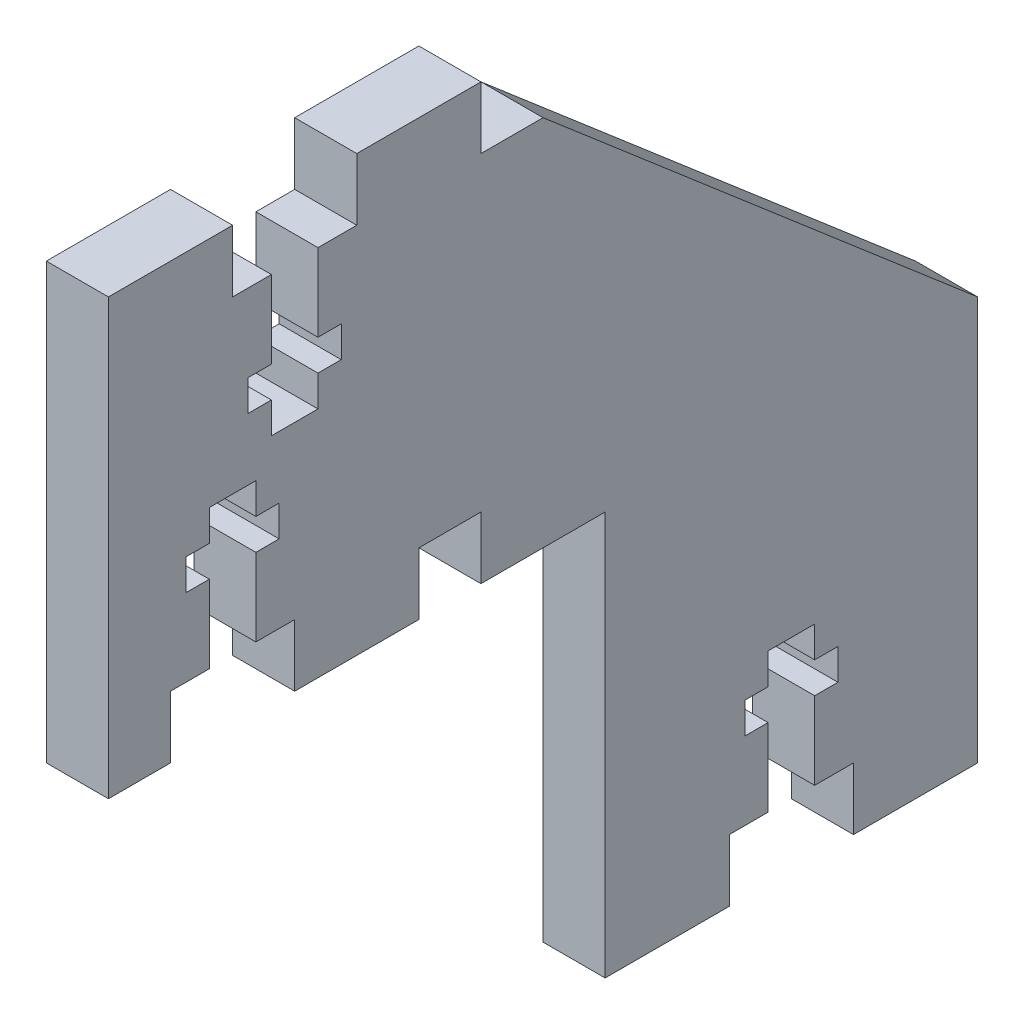
SolidWorks part; units mm, degrees
ref_plane "Front Plane" through (0, 0, 0) normal (0, 0, 1) x (1, 0, 0)
ref_plane "Top Plane" through (0, 0, 0) normal (0, 1, 0) x (1, 0, 0)
ref_plane "Right Plane" through (0, 0, 0) normal (1, 0, 0) x (0, 0, -1)
sketch "Sketch1" plane through (0, 0, 0) normal (1, 0, 0) x (0, 0, -1)
  line L0 (12.7, 44.45) -> (12.7, 38.1)
  line L1 (0, 0) -> (44.45, 0)
  line L2 (0, 0) -> (0, 44.45)
  line L3 (0, 44.45) -> (44.45, 44.45)
  line L4 (44.45, 0) -> (44.45, 44.45)
  line L5 (12.7, 38.1) -> (25.4, 38.1)
  line L6 (6.35, 0) -> (6.35, 6.35)
  line L7 (6.35, 6.35) -> (19.05, 6.35)
  line L8 (19.05, 6.35) -> (19.05, 0)
  line L9 (31.75, 0) -> (31.75, 6.35)
  line L10 (31.75, 6.35) -> (38.1, 6.35)
  line L11 (38.1, 6.35) -> (38.1, 0)
  line L12 (25.4, 38.1) -> (25.4, 44.45)
  line L13 (38.1, 44.45) -> (38.1, 38.1)
  line L14 (38.1, 38.1) -> (44.45, 38.1)
  line L15 (44.45, 0) -> (50.8, 0)
  line L16 (44.45, 38.1) -> (88.9, 0)
  line L17 (50.8, 0) -> (88.9, 0)
  line L18 (50.8, 0) -> (50.8, -34.925)
  line L19 (50.8, -34.925) -> (88.9, -34.925)
  line L20 (88.9, 0) -> (88.9, -34.925)
  line L22 (50.8, -34.925) -> (63.5, -34.925)
  line L23 (50.8, -34.925) -> (50.8, -41.275)
  line L24 (50.8, -41.275) -> (63.5, -41.275)
  line L25 (63.5, -34.925) -> (63.5, -41.275)
  line L26 (76.2, -34.925) -> (88.9, -34.925)
  line L27 (76.2, -34.925) -> (76.2, -41.275)
  line L28 (76.2, -41.275) -> (88.9, -41.275)
  line L29 (88.9, -34.925) -> (88.9, -41.275)
  dimension "D1" = 44.45
  dimension "D2" = 44.45
  dimension "D3" = 6.35
  dimension "D4" = 6.35
  dimension "D5" = 6.35
  dimension "D6" = 12.7
  dimension "D7" = 12.7
  dimension "D8" = 6.35
  dimension "D9" = 6.35
  dimension "D10" = 6.35
  dimension "D11" = 12.7
  dimension "D12" = 12.7
  dimension "D13" = 12.7
  dimension "D14" = 6.35
  dimension "D15" = 34.925
  dimension "D16" = 38.1
  dimension "D17" = 12.7
  dimension "D18" = 6.35
  dimension "D19" = 12.7
  dimension "D20" = 6.35
extrude "Boss-Extrude1" add sketch "Sketch1" along normal blind 6.35 contours L14 L13 L3 L12 L5 L0 L2 L1 L6 L7 L8 L9 L10 L11 L4 | L15 L17 L16 L4 | L25 L19 L23 L24 | L20 L17 L18 L19 | L26 L27 L28 L29
sketch "Sketch2" plane through (6.35, 0, 0) normal (1, 0, 0) x (0, 0, -1)
  line L0 (6.35, 6.35) -> (19.05, 6.35) construction
  line L1 (10.3187, 6.35) -> (15.0813, 6.35)
  line L2 (10.3187, 6.35) -> (10.3187, 20.6375)
  line L3 (10.3187, 20.6375) -> (15.0813, 20.6375)
  line L4 (15.0813, 6.35) -> (15.0813, 20.6375)
  line L5 (12.7, 38.1) -> (25.4, 38.1) construction
  line L6 (17.4625, 17.4625) -> (7.9375, 17.4625)
  line L7 (17.4625, 17.4625) -> (17.4625, 14.2875)
  line L8 (17.4625, 14.2875) -> (7.9375, 14.2875)
  line L9 (7.9375, 17.4625) -> (7.9375, 14.2875)
  line L10 (16.6687, 38.1) -> (21.4312, 38.1)
  line L11 (16.6687, 38.1) -> (16.6688, 23.8125)
  line L12 (16.6688, 23.8125) -> (21.4312, 23.8125)
  line L13 (21.4312, 38.1) -> (21.4312, 23.8125)
  line L14 (63.5, -34.925) -> (76.2, -34.925) construction
  line L15 (23.8125, 30.1625) -> (14.2875, 30.1625)
  line L16 (23.8125, 30.1625) -> (23.8125, 26.9875)
  line L17 (23.8125, 26.9875) -> (14.2875, 26.9875)
  line L18 (14.2875, 30.1625) -> (14.2875, 26.9875)
  line L19 (67.4688, -34.925) -> (72.2313, -34.925)
  line L20 (67.4688, -34.925) -> (67.4688, -20.6375)
  line L21 (67.4688, -20.6375) -> (72.2313, -20.6375)
  line L22 (72.2313, -34.925) -> (72.2313, -20.6375)
  line L23 (12.7, 44.45) -> (12.7, 38.1) construction
  line L24 (74.6125, -23.8125) -> (65.0875, -23.8125)
  line L25 (74.6125, -23.8125) -> (74.6125, -26.9875)
  line L26 (74.6125, -26.9875) -> (65.0875, -26.9875)
  line L27 (65.0875, -23.8125) -> (65.0875, -26.9875)
  line L28 (63.5, -34.925) -> (63.5, -41.275) construction
  dimension "D1" = 14.2875
  dimension "D2" = 4.7625
  dimension "D3" = 9.525
  dimension "D4" = 2.3813
  dimension "D5" = 3.175
  dimension "D6" = 3.175
  dimension "D7" = 14.2875
  dimension "D8" = 3.175
  dimension "D9" = 3.175
  dimension "D10" = 4.7625
  dimension "D11" = 9.525
  dimension "D12" = 2.3813
  dimension "D13" = 3.9688
  dimension "D14" = 3.9688
  dimension "D15" = 14.2875
  dimension "D16" = 3.175
  dimension "D17" = 3.175
  dimension "D18" = 4.7625
  dimension "D19" = 9.525
  dimension "D20" = 2.3813
  dimension "D21" = 3.9688
extrude "Cut-Extrude1" cut sketch "Sketch2" against normal blind 6.35 contours L13 L12 L11 L10 | L15 L18 L17 L16 | L8 L9 L6 L7 | L4 L3 L2 L1 | L24 L27 L26 L25 | L20 L21 L22 L19
